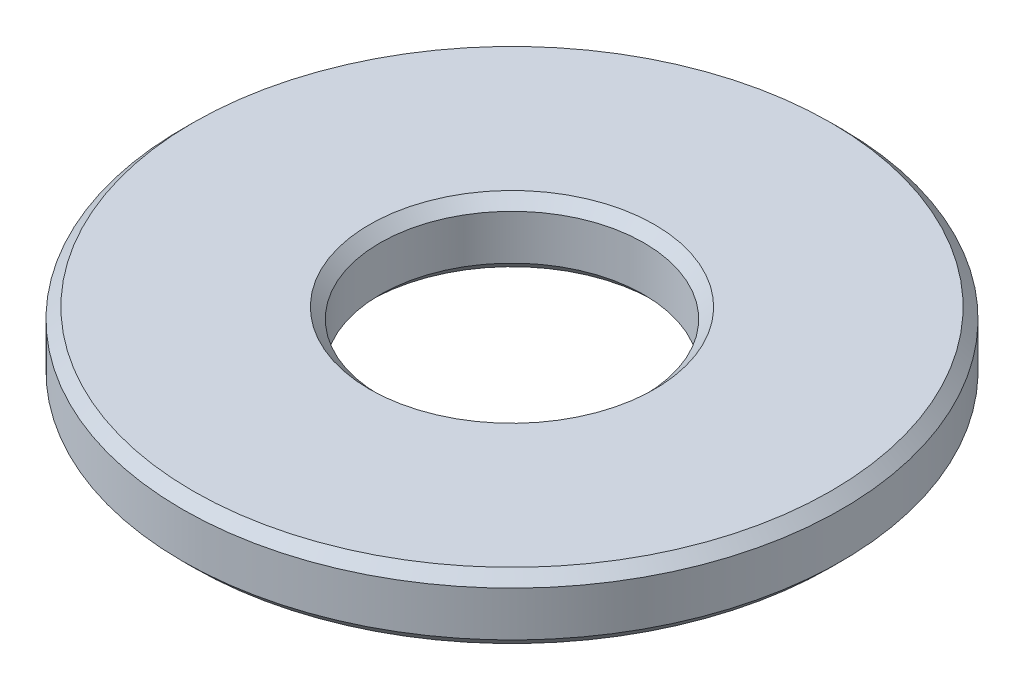
SolidWorks part; units mm, degrees
material "Rubber"
ref_plane "Front" through (0, 0, 0) normal (0, 0, 1) x (1, 0, 0)
ref_plane "Top" through (0, 0, 0) normal (0, 1, 0) x (1, 0, 0)
ref_plane "Right" through (0, 0, 0) normal (1, 0, 0) x (0, 0, -1)
sketch "Sketch1" plane through (0, 0, 0) normal (0, 0, 1) x (1, 0, 0)
  line L0 (0, 3.4096) -> (0, -3.4096) construction
  line L1 (1.5875, 0.3969) -> (1.5875, -0.3969)
  line L2 (1.5875, -0.3969) -> (3.9624, -0.3969)
  line L3 (3.9624, -0.3969) -> (3.9624, 0.3969)
  line L4 (3.9624, 0.3969) -> (1.5875, 0.3969)
  line L5 (1.5875, 0) -> (0, 0) construction
  dimension "D1" = 3.175
  dimension "D2" = 7.9248
  dimension "D3" = 0.7937
revolve "Revolve1" add sketch "Sketch1" angle 360 about L0
chamfer "Chamfer1" distance 0.127 angle 45 4 edges at (0, -0.3969, 3.9624) (0, 0.3969, 3.9624) (0, 0.3969, 1.5875) (0, -0.3969, 1.5875)
